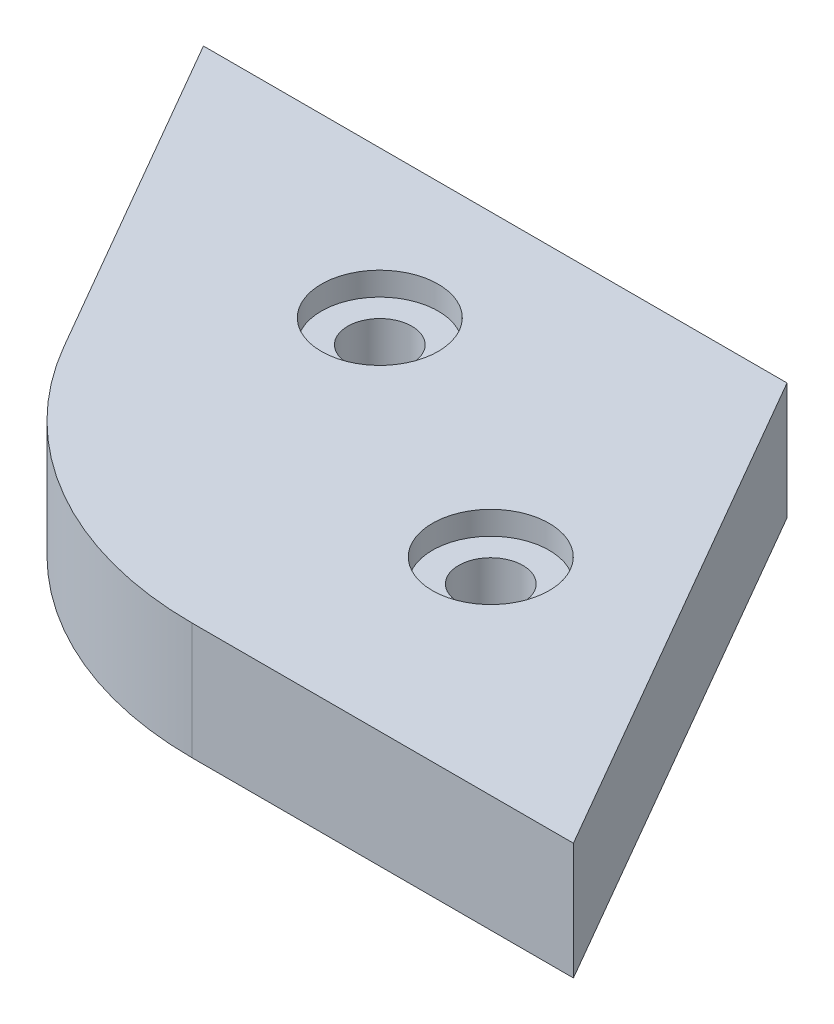
SolidWorks part; units mm, degrees
ref_plane "Alzado" through (0, 0, 0) normal (0, 0, 1) x (1, 0, 0)
ref_plane "Planta" through (0, 0, 0) normal (0, 1, 0) x (1, 0, 0)
ref_plane "Vista lateral" through (0, 0, 0) normal (1, 0, 0) x (0, 0, -1)
sketch "Croquis1" plane through (0, 0, 0) normal (0, 1, 0) x (1, 0, 0)
  line L5 (-148.724, -344.2) -> (-198.724, -344.2)
  line L6 (195.8372, -339.2) -> (391.6744, 0) construction
  line L11 (391.6744, 0) -> (195.8372, 339.2) construction
  line L12 (195.8372, 339.2) -> (-195.8372, 339.2) construction
  line L15 (-195.8372, 339.2) -> (-391.6744, 0) construction
  line L16 (-391.6744, 0) -> (-195.8372, -339.2) construction
  line L17 (-195.8372, -339.2) -> (195.8372, -339.2) construction
  line L18 (188.5049, -326.5) -> (377.0097, 0) construction
  line L19 (377.0097, 0) -> (188.5049, 326.5) construction
  line L20 (188.5049, 326.5) -> (-188.5049, 326.5) construction
  line L21 (-188.5049, 326.5) -> (-377.0097, 0) construction
  line L22 (-377.0097, 0) -> (-188.5049, -326.5) construction
  line L23 (-188.5049, -326.5) -> (188.5049, -326.5) construction
  line L24 (-198.724, -344.2) -> (-223.724, -300.8987)
  line L25 (-223.724, -300.8987) -> (-173.724, -300.8987)
  line L26 (-173.724, -300.8987) -> (-148.724, -344.2)
  line L27 (-198.724, -344.2) -> (-169.6, -293.7558) construction
  circle A5 centre (0, 0) radius 339.2 construction
  circle A6 centre (0, 0) radius 326.5 construction
  circle A7 centre (-173.5049, -326.5) radius 2.75
  circle A8 centre (-196.0049, -313.5096) radius 2.75
  point P0 (0, 0)
  dimension "D5" = 15
  dimension "D8" = 15
  dimension "D1" = 678.4
  dimension "D2" = 653
  dimension "D7" = 5.5
  dimension "D3" = 5
  dimension "D4" = 5
  dimension "D6" = 50
extrude "Saliente-Extruir1" add sketch "Croquis1" along normal blind 10
sketch "Croquis2" plane through (0, 10, 0) normal (0, 1, 0) x (1, 0, 0)
  circle A0 centre (-196.0049, -313.5096) radius 5
  circle A1 centre (-173.5049, -326.5) radius 5
  dimension "D1" = 10
extrude "Cortar-Extruir1" cut sketch "Croquis2" against normal blind 2
fillet "Redondeo1" radius 30 1 edges at (-198.724, 5, 344.2)
